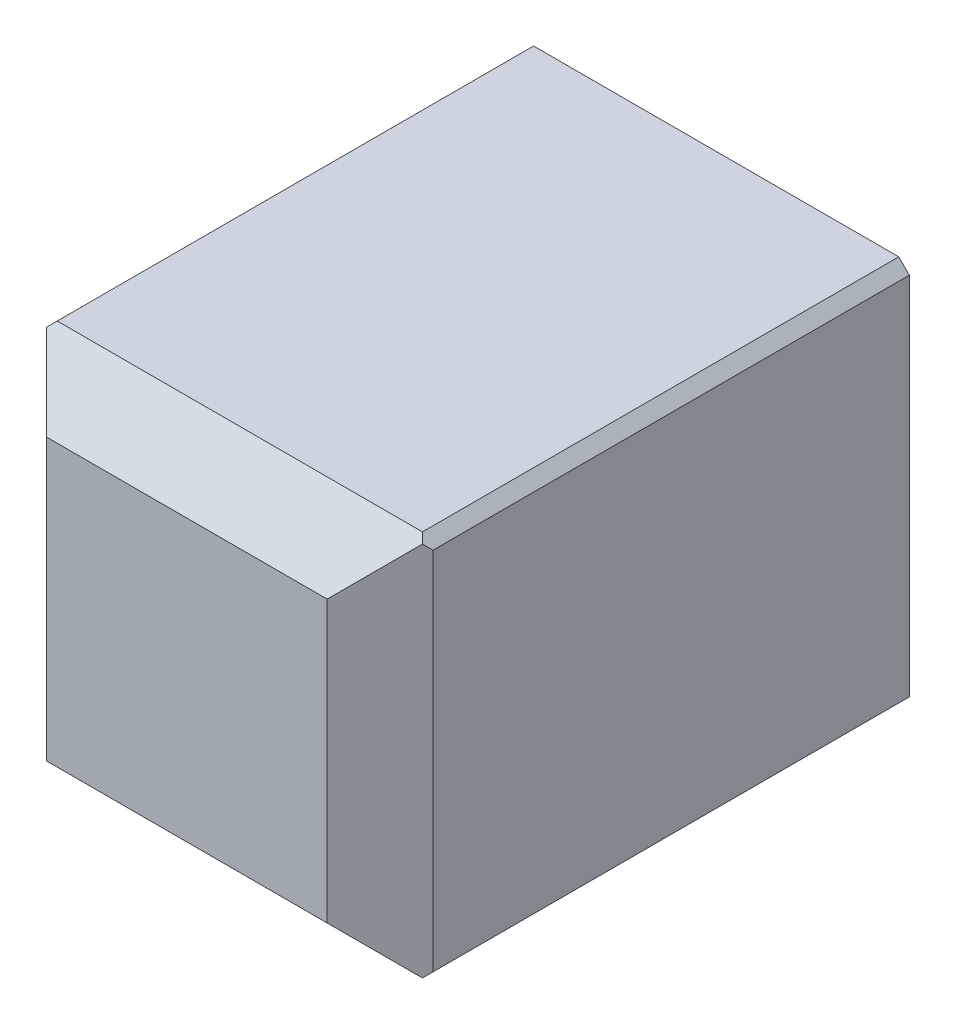
SolidWorks part; units mm, degrees
ref_plane "Front Plane" through (0, 0, 0) normal (0, 0, 1) x (1, 0, 0)
ref_plane "Top Plane" through (0, 0, 0) normal (0, 1, 0) x (1, 0, 0)
ref_plane "Right Plane" through (0, 0, 0) normal (1, 0, 0) x (0, 0, -1)
sketch "Sketch1" plane through (0, 0, 0) normal (0, 0, 1) x (1, 0, 0)
  line L1 (0, 0) -> (3.3, 0)
  line L2 (0, 0) -> (0, 3.3)
  line L3 (0, 3.3) -> (3.3, 3.3)
  line L4 (3.3, 0) -> (3.3, 3.3)
  line L9 (-2, 5.3) -> (5.3, 5.3)
  line L10 (-2, 5.3) -> (-2, -2)
  line L11 (-2, -2) -> (5.3, -2)
  line L12 (5.3, 5.3) -> (5.3, -2)
extrude "Boss-Extrude1" add sketch "Sketch1" along normal blind 8
sketch "Sketch3" plane through (0, 0, 8) normal (0, 0, 1) x (1, 0, 0)
  line L1 (-2, 5.3) -> (5.3, 5.3)
  line L2 (-2, 5.3) -> (-2, -2)
  line L3 (-2, -2) -> (5.3, -2)
  line L4 (5.3, 5.3) -> (5.3, -2)
extrude "Boss-Extrude2" add sketch "Sketch3" along normal blind 2
chamfer "Chamfer1" distance 1 angle 45 4 edges at (1.65, 5.3, 10) (5.3, 1.65, 10) (1.65, -2, 10) (-2, 1.65, 10)
chamfer "Chamfer2" distance 0.2 angle 45 4 edges at (5.3, -2, 4.5) (5.3, 5.3, 4.5) (-2, 5.3, 4.5) (-2, -2, 4.5)
